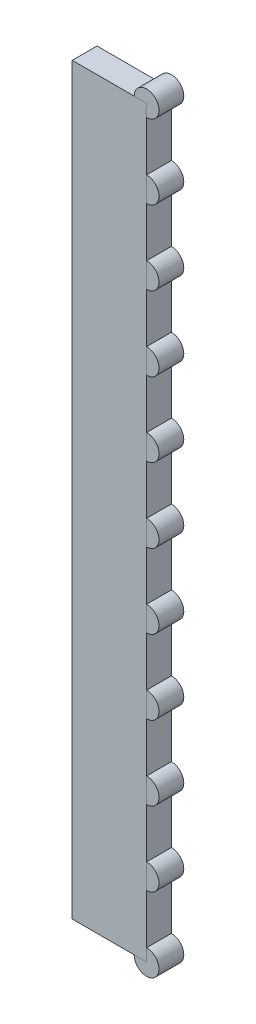
SolidWorks part; units mm, degrees
ref_plane "Front Plane" through (0, 0, 0) normal (0, 0, 1) x (1, 0, 0)
ref_plane "Top Plane" through (0, 0, 0) normal (0, 1, 0) x (1, 0, 0)
ref_plane "Right Plane" through (0, 0, 0) normal (1, 0, 0) x (0, 0, -1)
sketch "Sketch1" plane through (0, 0, 0) normal (1, 0, 0) x (0, 0, -1)
  line L0 (0, 0) -> (0, 300)
  dimension "D1" = 300
sketch "Sketch2" plane through (0, 0, 0) normal (0, 0, 1) x (1, 0, 0)
  line L0 (0, 0) -> (0, 300) construction
  line L1 (0, 300) -> (30, 300)
  line L2 (0, 300) -> (0, 0)
  line L3 (0, 0) -> (30, 0)
  line L4 (30, 300) -> (30, 0)
  dimension "D1" = 30
extrude "Boss-Extrude1" add sketch "Sketch2" along normal blind 10
sketch "Sketch3" plane through (0, 0, 10) normal (0, 0, 1) x (1, 0, 0)
  circle A0 centre (30, 300) radius 5
  circle A1 centre (30, 270) radius 5
  circle A2 centre (30, 240) radius 5
  circle A3 centre (30, 210) radius 5
  circle A4 centre (30, 180) radius 5
  circle A5 centre (30, 150) radius 5
  circle A6 centre (30, 120) radius 5
  circle A7 centre (30, 90) radius 5
  circle A8 centre (30, 60) radius 5
  circle A9 centre (30, 30) radius 5
  circle A10 centre (30, 0) radius 5
  dimension "D1" = 10
  dimension "D2" = 11
extrude "Boss-Extrude2" add sketch "Sketch3" against normal blind 10 separate body
